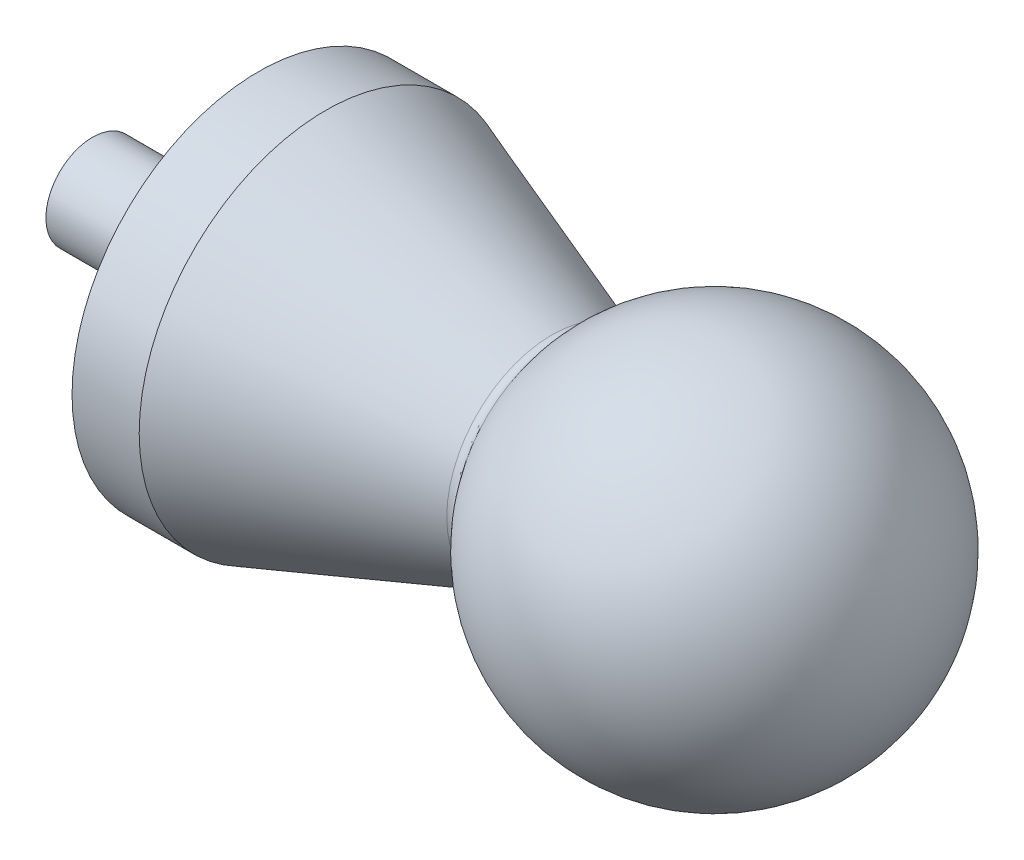
SolidWorks part; units mm, degrees
material "Brass"
ref_plane "Front" through (0, 0, 0) normal (0, 0, 1) x (1, 0, 0)
ref_plane "Top" through (0, 0, 0) normal (0, 1, 0) x (1, 0, 0)
ref_plane "Right" through (0, 0, 0) normal (1, 0, 0) x (0, 0, -1)
sketch "Sketch1" plane through (0, 0, 0) normal (0, 1, 0) x (1, 0, 0)
  line L0 (-50, 0) -> (50, 0) construction
  line L1 (0, 0) -> (-133.3333, 0) construction
  line L2 (0, 0) -> (0, 10) construction
  line L3 (0, 10) -> (-133.3333, 10) construction
  line L4 (-133.3333, 0) -> (-133.3333, 10) construction
  line L5 (25.0028, 0) -> (-54.8539, 0) construction
  line L6 (0, 0) -> (-83.3333, 0) construction
  line L7 (0, 0) -> (0, 40) construction
  line L8 (0, 40) -> (-83.3333, 40) construction
  line L9 (-83.3333, 0) -> (-83.3333, 40) construction
  line L10 (-83.3333, 40) -> (-33.3925, 22.0213)
  line L11 (-133.3333, 0) -> (-133.3333, 10)
  line L12 (-83.3333, 40) -> (-97.7333, 40) construction
  line L13 (-83.3333, 40) -> (-83.3333, 0) construction
  line L14 (-83.3333, 0) -> (-97.7333, 0) construction
  line L15 (-97.7333, 40) -> (-97.7333, 0) construction
  line L16 (-133.3333, 10) -> (-97.7333, 10)
  line L17 (-97.7333, 10) -> (-97.7333, 40)
  line L18 (-97.7333, 40) -> (-83.3333, 40)
  line L19 (-133.3333, 0) -> (40, 0)
  arc A0 (40, 0) -> (-33.3925, 22.0213) centre (0, 0) ccw
  dimension "D1" = 40
revolve "Revolve1" add sketch "Sketch1" angle 360 about L5
fillet "Fillet1" radius 2 1 edges at (-33.3925, 0, -22.0213)
